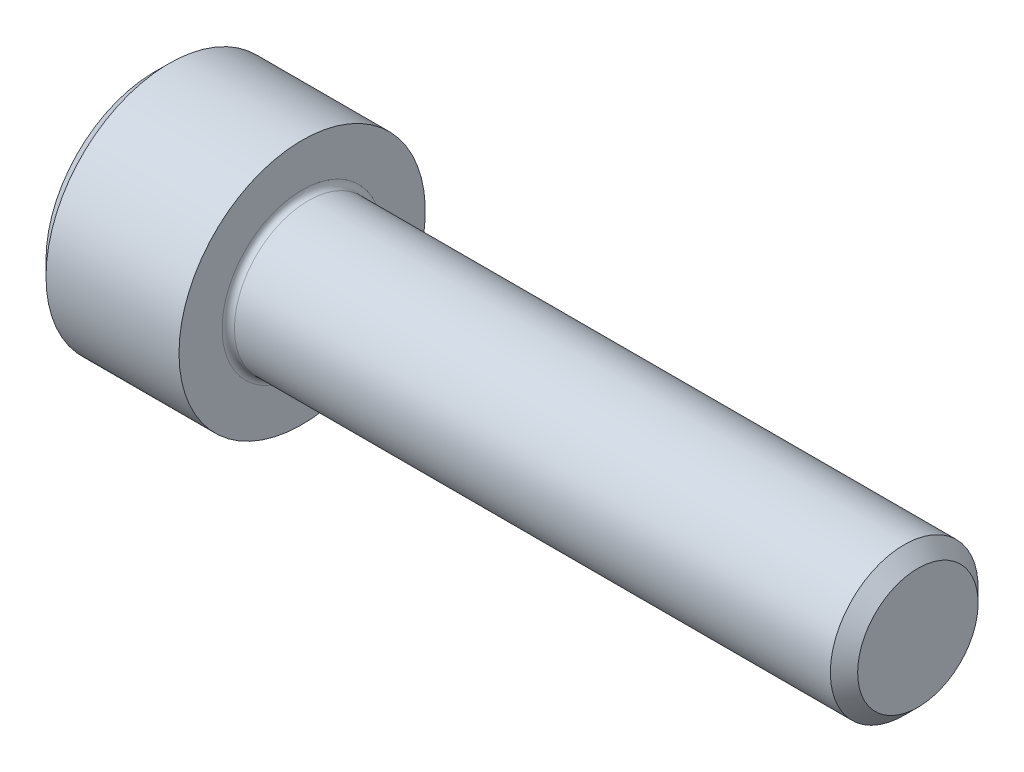
SolidWorks part; units mm, degrees
revolve "Base-Revolve" add sketch "BodySke"
sketch "BodySke" plane through (0, 0, 0) normal (0, 0, 1) x (1, 0, 0)
  line L0 (0, 0) -> (0, 4.4)
  line L1 (0.6, 5) -> (6, 5)
  line L2 (6, 5) -> (6, 3)
  line L3 (6, 3) -> (30.4455, 3)
  line L4 (31, 2.4455) -> (31, 0)
  line L5 (31, 0) -> (0, 0)
  line L6 (-31.75, 0) -> (127, 0) construction
  line L7 (0, 4.4) -> (0.6, 5)
  line L8 (31, 2.4455) -> (30.4455, 3)
  line L9 (0, -4.4) -> (0.6, -5) construction
  line L10 (31, -2.4455) -> (30.4455, -3) construction
  line L11 (7, 9.525) -> (7, 3.175) construction
  line L12 (6, 9.525) -> (6, 3.175) construction
  line L13 (-19, 9.525) -> (-19, 3.175) construction
  dimension "Diameter" = 6
  dimension "Head_ht" = 6
  dimension "Length" = 25
  dimension "Body_ch_ang" = 45
  dimension "Head_dia" = 10
  dimension "Head_ch_ang" = 45
  dimension "Minor_dia" = 4.891
  dimension "Advance" = 1
  dimension "Thread_nom" = 25
  dimension "Thread_length" = 50
  dimension "Head_ch_ht" = 0.6
cosmetic thread "ThreadCosmetic" [suppressed]
fillet "Fillet1" radius 0.25 1 edges at (6, 0, 3)
ref_plane "Plane1" through (0, 0, 0) normal (0, 0, 1) x (1, 0, 0)
ref_plane "Plane2" through (0, 0, 0) normal (0, 1, 0) x (1, 0, 0)
ref_plane "Plane3" through (0, 0, 0) normal (1, 0, 0) x (0, 0, -1)
sketch "Sketch2" plane through (0, 0, 0) normal (0, 0, 1) x (1, 0, 0)
  line L0 (0, 2.542) -> (3, 2.542)
  line L1 (3, 2.542) -> (4.4676, 0)
  line L2 (-31.75, 0) -> (127, 0) construction
  line L3 (4.4676, 0) -> (0, 0)
  line L4 (0, 0) -> (0, 2.542)
  line L5 (0, 4.4) -> (0, -4.4) construction
  line L6 (0, 0) -> (47.625, 0) construction
  line L7 (6, -5) -> (6, 5) construction
  dimension "D1" = 2.542
  dimension "D2" = 60
revolve "Hex-PreBroach" cut sketch "Sketch2" angle 360 about L6
sketch "Sketch3" plane through (0, 0, 0) normal (-1, 0, 0) x (0, 0.5, 0.866)
  line L0 (1.4676, 2.542) -> (-1.4676, 2.542)
  line L1 (-1.4676, 2.542) -> (-2.9352, 0)
  line L2 (1.4676, 2.542) -> (2.9352, 0)
  line L3 (1.4676, -2.542) -> (2.9352, 0)
  line L4 (1.4676, -2.542) -> (-1.4676, -2.542)
  line L5 (-1.4676, -2.542) -> (-2.9352, 0)
  dimension "D1" = 2.542
  dimension "D2" = 2.542
  dimension "Hex_size" = 5.084
extrude "Hex" cut sketch "Sketch3" against normal blind 3
sketch "Sketch4" plane through (0, 0, 0) normal (-1, 0, 0) x (0, 0, 1)
  line L0 (0, 0) -> (2.8067, 0)
  line L1 (0, 0) -> (6.1484, 3.5498) construction
  line L2 (0, 0) -> (1.4033, 2.4307)
  line L3 (2.3336, 0.614) -> (2.6851, 0.817)
  line L4 (1.6986, 1.7139) -> (2.0501, 1.9169)
  arc A0 (2.3336, 0.614) -> (1.6986, 1.7139) centre (0, 0) ccw
  arc A1 (2.8067, 0) -> (2.6851, 0.817) centre (0, 0) ccw
  arc A2 (1.4033, 2.4307) -> (2.0501, 1.9169) centre (0, 0) cw
  dimension "D1" = 30
  dimension "D2" = 60
  dimension "Spline_p_dim" = 1.27
  dimension "D3" = 0.635
extrude "Spline" [suppressed] cut sketch "Sketch4" against normal blind 3
pattern_circular "CirPattern1" [suppressed] count 6 every 60
sketch "Sketch5" plane through (0, 0, 0) normal (0, 0, 1) x (1, 0, 0)
  line L0 (-31.75, 0) -> (127, 0) construction
  line L2 (0, 4.4) -> (0, -4.4) construction
  circle A0 centre (2.3, 0) radius 0.675
  dimension "Drilled_hole_dia" = 1.35
  dimension "Drilled_hole_loc" = 2.3
extrude "Hole" [suppressed] cut sketch "Sketch5" against normal through all and the other way through all
pattern_circular "Drilled-4" [suppressed] count 2 every 60
pattern_circular "Drilled-6" [suppressed] count 3 every 60
sketch "ThdSchSke" plane through (0, 0, 0) normal (0, 0, 1) x (1, 0, 0)
  line L0 (7, -2.4455) -> (6.6117, -3)
  line L1 (7, -2.4455) -> (7.3883, -3)
  line L2 (7.3883, -3) -> (7.3883, -3.75)
  line L3 (-3.175, 0) -> (5.1513, 0) construction
  line L5 (7.3883, -3.75) -> (6.6117, -3.75)
  line L6 (6.6117, -3.75) -> (6.6117, -3)
  line L7 (0, 4.4) -> (0, -4.4) construction
  dimension "Thread_minor" = 4.891
  dimension "Diameter" = 6
  dimension "Start" = 7
revolve "ThreadSchematic" [suppressed] cut sketch "ThdSchSke" angle 360 about L3
pattern_linear "ThdSchPat" [suppressed]
equation "\"D2@Sketch3\" = \"Hex_size@Sketch3\" / 2"
equation "\"D1@Sketch3\" = \"Hex_size@Sketch3\" / 2"
equation "\"D1@Sketch2\" = \"Hex_size@Sketch3\" / 2"
equation "\"D3@Sketch4\" = \"Spline_p_dim@Sketch4\" / 2"
equation "\"Thread_minor@ThreadCosmetic\"  =  \"Minor_dia@BodySke\""
equation "\"D2@CirPattern1\" = 360 / \"Num_teeth@CirPattern1\""
equation "\"Wall_thickness@Sketch2\" = \"Head_ht@BodySke\" - \"Key_eng@Hex\""
equation "\"Thread_length@ThreadCosmetic\" = ((sgn( (\"Length@BodySke\" - \"Advance@BodySke\" ) - \"Thread_nom@BodySke\" )-1)*( (\"Length@BodySke\" - \"Advance@BodySke\" ) - \"Thread_nom@BodySke\" ))/-2+ \"Thread_nom@BodySke\""
equation "\"Thread_minor@ThdSchSke\" = \"Minor_dia@BodySke\""
equation "\"Diameter@ThdSchSke\" = \"Diameter@BodySke\""
equation "\"Overcut@ThdSchSke\" = \"Diameter@BodySke\" * 1.25"
equation "\"Start@ThdSchSke\" = \"Head_ht@BodySke\" + \"Length@BodySke\" - \"Thread_length@ThreadCosmetic\"  '---Non-countersunk---"
equation "\"Num_threads@ThdSchPat\" = int( \"Thread_length@ThreadCosmetic\" / \"Advance@BodySke\" + 0.999 )  + 1"
equation "\"Advance@ThdSchPat\" = \"Thread_length@ThreadCosmetic\" /  (\"Num_threads@ThdSchPat\" - 1) 'relax it"
equation "\"Num_threads@ThdSchPat\" = \"Num_threads@ThdSchPat\" - sgn( \"Num_threads@ThdSchPat\" - 1) '---chamfered tips only---"
